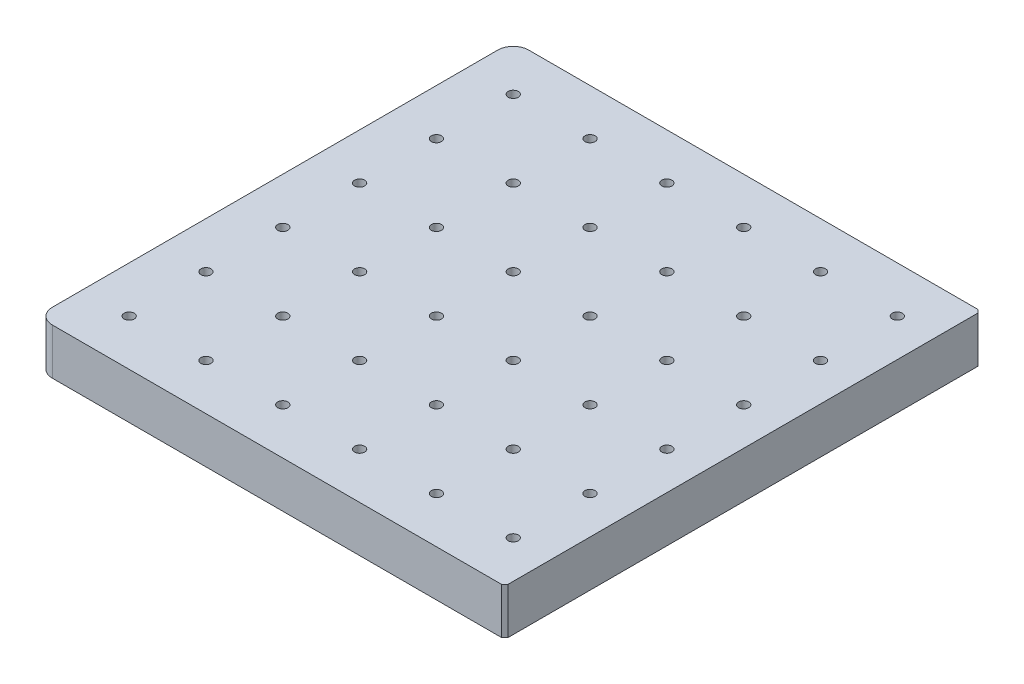
SolidWorks part; units mm, degrees
ref_plane "Front Plane" through (0, 0, 0) normal (0, 0, 1) x (1, 0, 0)
ref_plane "Top Plane" through (0, 0, 0) normal (0, 1, 0) x (1, 0, 0)
ref_plane "Right Plane" through (0, 0, 0) normal (1, 0, 0) x (0, 0, -1)
sketch "Sketch1" plane through (0, 0, 0) normal (0, 1, 0) x (1, 0, 0)
  line L1 (76.125, 77.5) -> (-76.125, 77.5)
  line L2 (76.125, 77.5) -> (76.125, -77.5)
  line L3 (76.125, -77.5) -> (-76.125, -77.5)
  line L4 (-76.125, 77.5) -> (-76.125, -77.5)
  line L5 (76.125, 77.5) -> (-76.125, -77.5) construction
  line L6 (76.125, -77.5) -> (-76.125, 77.5) construction
  point P0 (0, 0)
  dimension "D1" = 155
  dimension "D2" = 152.25
extrude "Boss-Extrude1" add sketch "Sketch1" along normal blind 15
sketch "Sketch2" plane through (0, 15, 0) normal (0, 1, 0) x (1, 0, 0)
  line L0 (-76.125, 77.5) -> (-76.125, -77.5) construction
  line L1 (-76.125, -77.5) -> (76.125, -77.5) construction
  circle A0 centre (-61.125, -62.5) radius 1.65
  dimension "D1" = 3.3
  dimension "D2" = 15
  dimension "D3" = 15
extrude "Cut-Extrude1" cut sketch "Sketch2" against normal through all
fillet "Fillet1" radius 5 2 edges at (-76.125, 7.5, 77.5) (-76.125, 7.5, -77.5)
chamfer "Chamfer1" distance 1 angle 45 2 edges at (76.125, 7.5, 77.5) (76.125, 7.5, -77.5)
ref_plane "Plane1" through (0, 6, 0) normal (0, -1, 0) x (-1, 0, 0)
sketch "Sketch3" plane through (0, 6, 0) normal (0, -1, 0) x (-1, 0, 0)
  line L1 (64.5891, -62.5) -> (62.8571, -59.5)
  line L2 (62.8571, -59.5) -> (59.3929, -59.5)
  line L3 (59.3929, -59.5) -> (57.6609, -62.5)
  line L4 (57.6609, -62.5) -> (59.3929, -65.5)
  line L5 (59.3929, -65.5) -> (62.8571, -65.5)
  line L6 (62.8571, -65.5) -> (64.5891, -62.5)
  circle A0 centre (61.125, -62.5) radius 3 construction
  dimension "D1" = 6
extrude "Cut-Extrude2" cut sketch "Sketch3" against normal blind 3
pattern_linear "LPattern1" count 6 spacing 25 along (1, 0, 0) of "Cut-Extrude2", "Cut-Extrude1"
pattern_linear "LPattern2" count 6 spacing 25 along (0, 0, -1) of "LPattern1", "Cut-Extrude1", "Cut-Extrude2"
